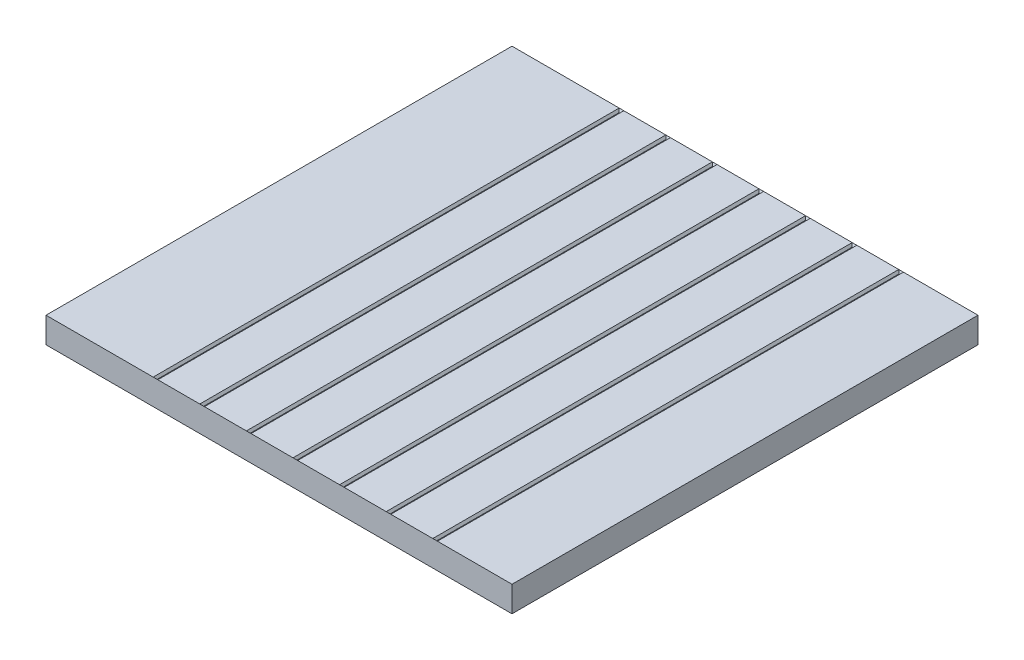
SolidWorks part; units mm, degrees
ref_plane "Front Plane" through (0, 0, 0) normal (0, 0, 1) x (1, 0, 0)
ref_plane "Top Plane" through (0, 0, 0) normal (0, 1, 0) x (1, 0, 0)
ref_plane "Right Plane" through (0, 0, 0) normal (1, 0, 0) x (0, 0, -1)
sketch "Sketch1" plane through (0, 0, 0) normal (0, 1, 0) x (1, 0, 0)
  line L1 (0, 0) -> (20, 0)
  line L2 (0, 0) -> (0, 20)
  line L3 (0, 20) -> (20, 20)
  line L4 (20, 0) -> (20, 20)
extrude "Boss-Extrude2" add sketch "Sketch1" along normal blind 1.1 contours L2 L3 L4 L1
sketch "Sketch2" plane through (0, 1.1, 0) normal (0, 1, 0) x (1, 0, 0)
  line L0 (20, 0) -> (16.7, 0) construction
  line L1 (0, 0) -> (20, 0) construction
  line L2 (16.8, 0) -> (16.8, 20)
  line L3 (0, 20) -> (20, 20) construction
  line L4 (16.6, 0) -> (16.6, 20)
  line L5 (14.8, 0) -> (14.8, 20)
  line L6 (14.6, 0) -> (14.6, 20)
  line L7 (12.8, 0) -> (12.8, 20)
  line L8 (12.6, 0) -> (12.6, 20)
  line L9 (10.8, 0) -> (10.8, 20)
  line L10 (10.6, 0) -> (10.6, 20)
  line L11 (8.8, 0) -> (8.8, 20)
  line L12 (8.6, 0) -> (8.6, 20)
  line L13 (6.8, 0) -> (6.8, 20)
  line L14 (6.6, 0) -> (6.6, 20)
  line L15 (4.8, 0) -> (4.8, 20)
  line L16 (4.6, 0) -> (4.6, 20)
  line L17 (4.6, 0) -> (4.8, 0)
  line L18 (6.6, 0) -> (6.8, 0)
  line L19 (8.6, 0) -> (8.8, 0)
  line L20 (10.6, 0) -> (10.8, 0)
  line L21 (12.6, 0) -> (12.8, 0)
  line L22 (14.6, 0) -> (14.8, 0)
  line L23 (16.6, 0) -> (16.8, 0)
  line L24 (4.6, 20) -> (4.8, 20)
  line L25 (6.6, 20) -> (6.8, 20)
  line L26 (8.6, 20) -> (8.8, 20)
  line L27 (10.6, 20) -> (10.8, 20)
  line L28 (12.6, 20) -> (12.8, 20)
  line L29 (14.6, 20) -> (14.8, 20)
  line L30 (16.6, 20) -> (16.8, 20)
  dimension "D1" = 3.3
  dimension "D2" = 0.1
  dimension "D3" = 0.1
  dimension "D4" = 7
extrude "Cut-Extrude1" cut sketch "Sketch2" along direction (0, -1, 0) on the side against the normal blind 0.1 draft 35
